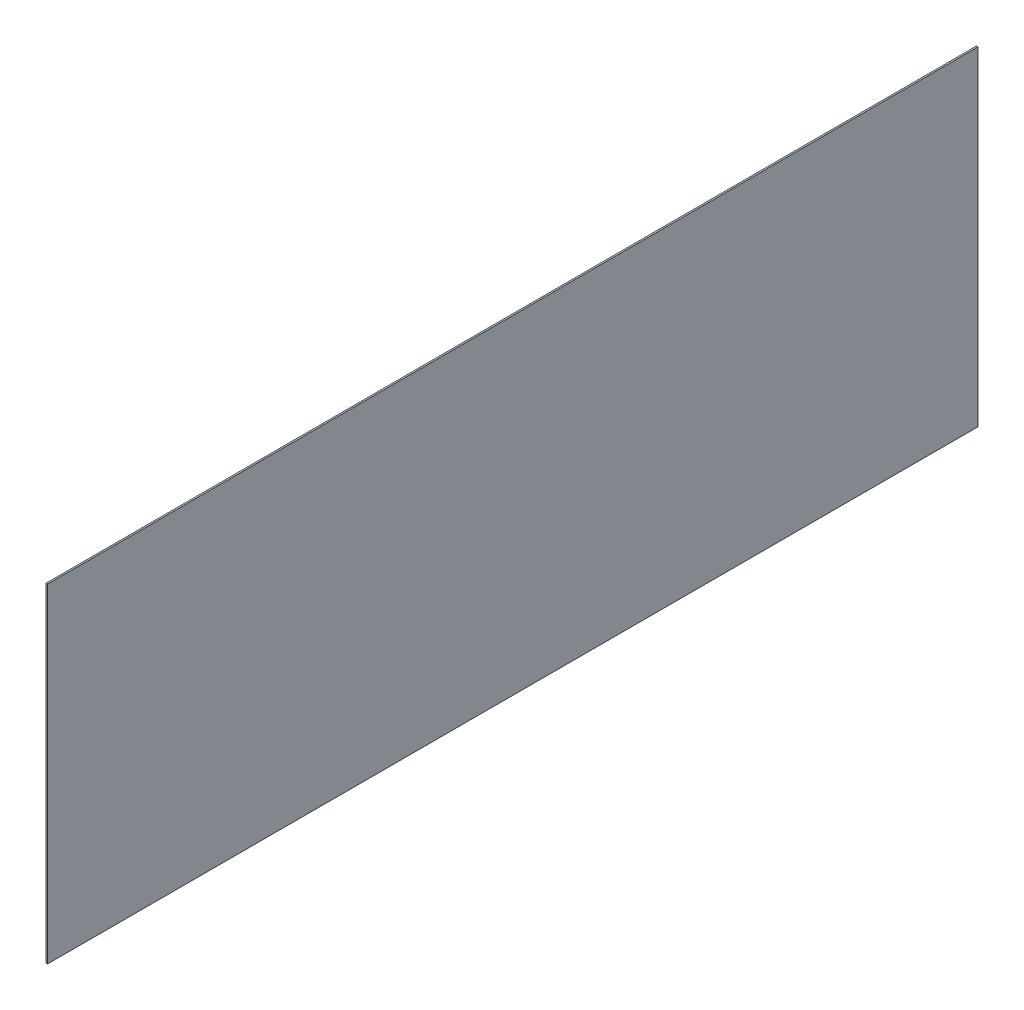
SolidWorks part; units mm, degrees
ref_plane "前视基准面" through (0, 0, 0) normal (0, 0, 1) x (1, 0, 0)
ref_plane "上视基准面" through (0, 0, 0) normal (0, 1, 0) x (1, 0, 0)
ref_plane "右视基准面" through (0, 0, 0) normal (1, 0, 0) x (0, 0, -1)
sketch "草图1" plane through (0, 0, 0) normal (1, 0, 0) x (0, 0, -1)
  line L1 (0, 0) -> (6000, 0)
  line L2 (0, 0) -> (0, 2121.32)
  line L3 (0, 2121.32) -> (6000, 2121.32)
  line L4 (6000, 0) -> (6000, 2121.32)
  dimension "D1" = 6000
  dimension "D2" = 2121.32
extrude "凸台-拉伸1" add sketch "草图1" along normal blind 10
